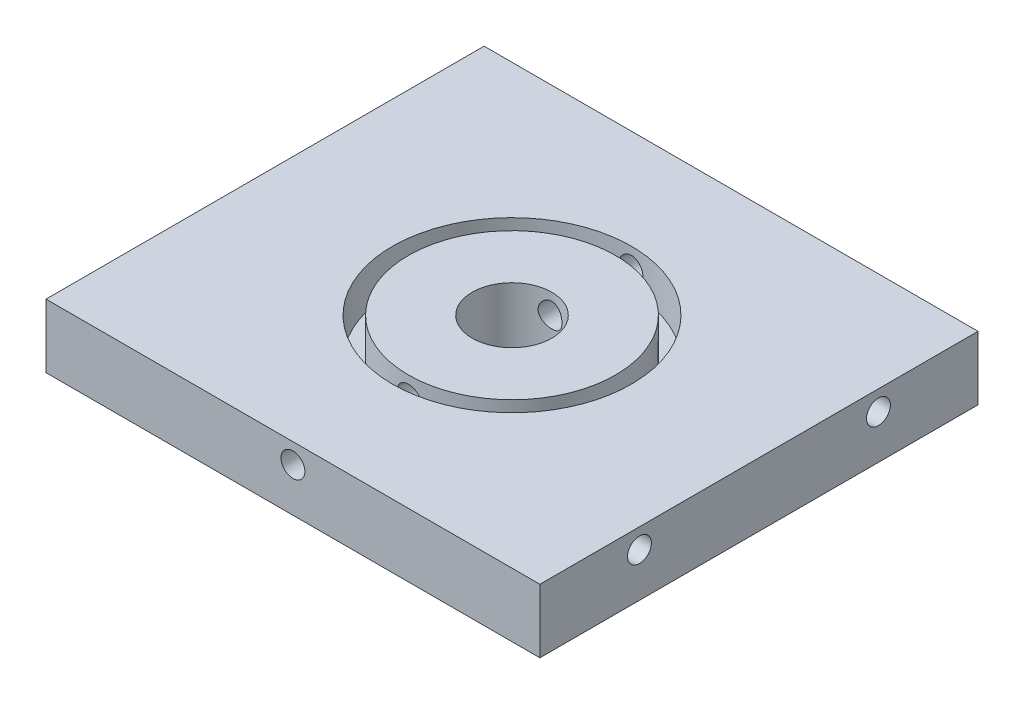
SolidWorks part; units mm, degrees
material "PLA"
ref_plane "Plan de face" through (0, 0, 0) normal (0, 0, 1) x (1, 0, 0)
ref_plane "Plan de dessus" through (0, 0, 0) normal (0, 1, 0) x (1, 0, 0)
ref_plane "Plan de droite" through (0, 0, 0) normal (1, 0, 0) x (0, 0, -1)
sketch "Esquisse1" plane through (0, 0, 0) normal (0, 0, 1) x (1, 0, 0)
  line L0 (-5.5, -49) -> (56.5, -49) construction
  line L5 (-5.5, -45) -> (56.5, -45)
  line L6 (-5.5, -45) -> (-5.5, -53)
  line L7 (-5.5, -53) -> (56.5, -53)
  line L8 (56.5, -45) -> (56.5, -53)
  line L9 (25.5, -45) -> (25.5, -53) construction
  dimension "D1" = 8
  dimension "D2" = 62
extrude "Boss.-Extru.1" add sketch "Esquisse1" along normal blind 55
sketch "Esquisse2" plane through (0, -45, 0) normal (0, 1, 0) x (-1, 0, 0)
  line L0 (5.5, 55) -> (-56.5, 55) construction
  line L7 (-56.5, 55) -> (-56.5, 0) construction
  circle A0 centre (-25.5, 27.5) radius 15
  circle A2 centre (-25.5, 27.5) radius 13
  dimension "D10" = 31
  dimension "D11" = 27.5
extrude "Enlèv. mat.-Extru.1" cut sketch "Esquisse2" against normal blind 5
sketch "Esquisse3" plane through (-5.5, 0, 0) normal (-1, 0, 0) x (0, 0, 1)
  line L0 (55, -53) -> (0, -53) construction
  line L1 (0, -45) -> (0, -53) construction
  line L2 (55, -45) -> (55, -53) construction
  circle A0 centre (12.5, -47.5) radius 1.5
  circle A1 centre (42.5, -47.5) radius 1.5
  dimension "D1" = 5.5
  dimension "D2" = 5.5
  dimension "D3" = 12.5
  dimension "D4" = 12.5
extrude "Enlèv. mat.-Extru.2" cut sketch "Esquisse3" against normal blind 10
sketch "Esquisse4" plane through (56.5, 0, 0) normal (1, 0, 0) x (0, 0, -1)
  line L0 (-55, -53) -> (0, -53) construction
  line L1 (-55, -45) -> (-55, -53) construction
  line L2 (0, -45) -> (0, -53) construction
  circle A0 centre (-42.5, -47.5) radius 1.5
  circle A1 centre (-12.5, -47.5) radius 1.5
  dimension "D1" = 5.5
  dimension "D2" = 5.5
  dimension "D3" = 12.5
  dimension "D4" = 12.5
extrude "Enlèv. mat.-Extru.3" cut sketch "Esquisse4" against normal blind 10
sketch "Esquisse5" plane through (0, 0, 0) normal (0, 0, -1) x (-1, 0, 0)
  line L0 (5.5, -45) -> (-56.5, -45) construction
  line L1 (-56.5, -45) -> (-56.5, -53) construction
  circle A0 centre (-25.5, -47.5) radius 1.5
  dimension "D1" = 2.5
  dimension "D2" = 31
extrude "Enlèv. mat.-Extru.4" cut sketch "Esquisse5" against normal through all
sketch "Esquisse6" plane through (0, -45, 0) normal (0, 1, 0) x (1, 0, 0)
  line L0 (-5.5, -55) -> (-5.5, 0) construction
  line L1 (-5.5, -55) -> (56.5, -55) construction
  circle A0 centre (25.5, -27.5) radius 5
  dimension "D1" = 31
  dimension "D2" = 27.5
extrude "Enlèv. mat.-Extru.5" cut sketch "Esquisse6" against normal through all contours A0
